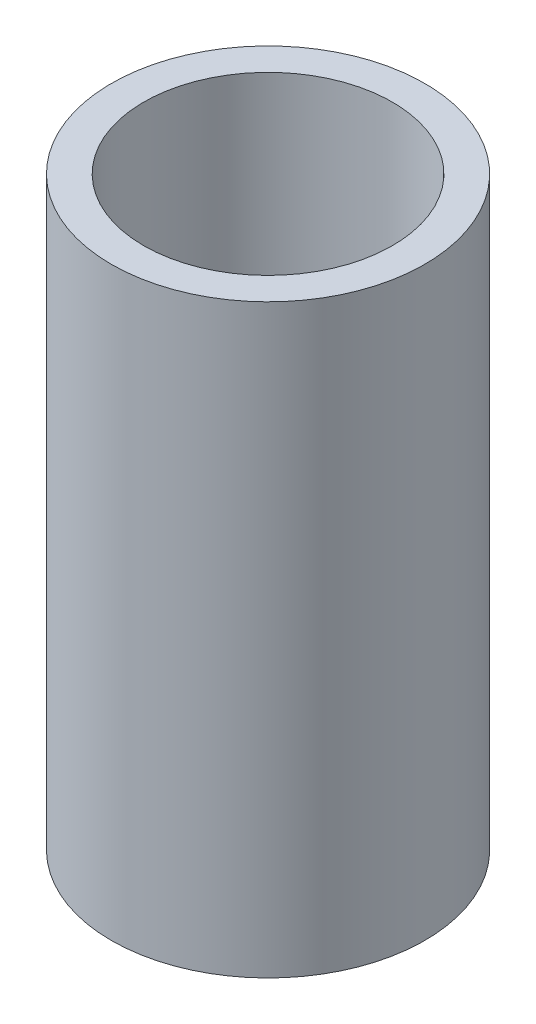
SolidWorks part; units mm, degrees
ref_plane "Front Plane" through (0, 0, 0) normal (0, 0, 1) x (1, 0, 0)
ref_plane "Top Plane" through (0, 0, 0) normal (0, 1, 0) x (1, 0, 0)
ref_plane "Right Plane" through (0, 0, 0) normal (1, 0, 0) x (0, 0, -1)
sketch "Sketch1" plane through (0, 0, 0) normal (0, 1, 0) x (1, 0, 0)
  circle A0 centre (0, 0) radius 3.175
  circle A1 centre (0, 0) radius 4
  dimension "D1" = 6.35
  dimension "D2" = 8
extrude "Boss-Extrude1" add sketch "Sketch1" along normal blind 14.948
